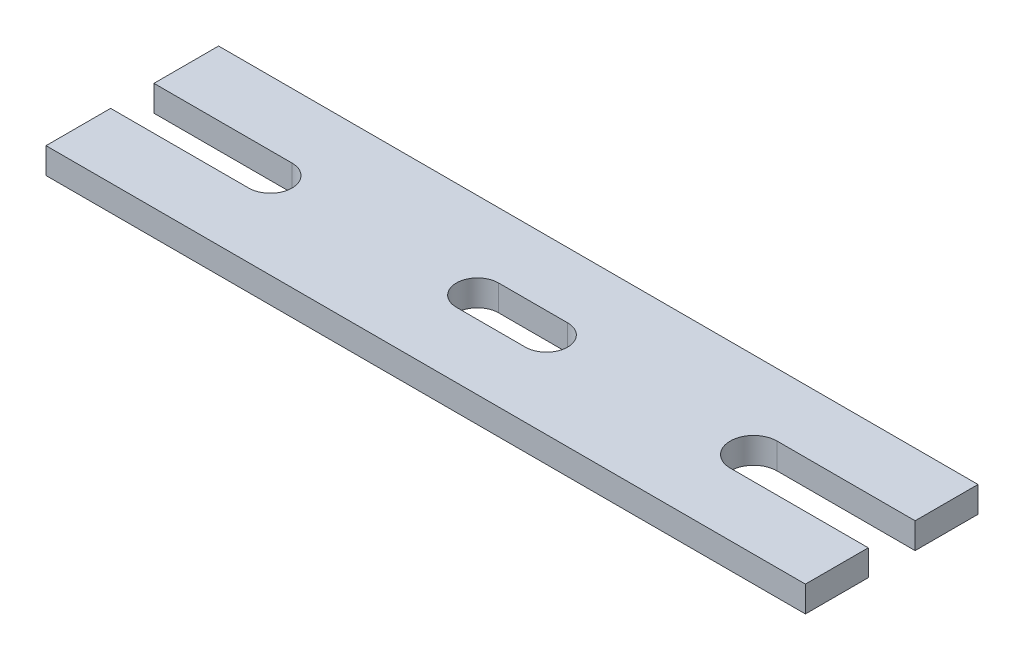
SolidWorks part; units mm, degrees
material "Plain Carbon Steel"
ref_plane "Front Plane" through (0, 0, 0) normal (0, 0, 1) x (1, 0, 0)
ref_plane "Top Plane" through (0, 0, 0) normal (0, 1, 0) x (1, 0, 0)
ref_plane "Right Plane" through (0, 0, 0) normal (1, 0, 0) x (0, 0, -1)
ref_plane "Plane12" through (88.9, 0, 0) normal (1, 0, 0) x (0, 0, -1)
ref_plane "Plane13" through (-88.9, 0, 0) normal (1, 0, 0) x (0, 0, -1)
sketch "Sketch1" plane through (0, 0, 0) normal (0, 1, 0) x (1, 0, 0)
  line L0 (-139.7, 0) -> (139.7, 0) construction
  line L1 (-139.7, 31.75) -> (139.7, 31.75)
  line L2 (-139.7, 31.75) -> (-139.7, -31.75)
  line L3 (-139.7, -31.75) -> (139.7, -31.75)
  line L4 (139.7, 31.75) -> (139.7, -31.75)
  line L5 (-139.7, 31.75) -> (139.7, -31.75) construction
  line L6 (-139.7, -31.75) -> (139.7, 31.75) construction
  point P0 (0, 0)
  dimension "D1" = 279.4
  dimension "D2" = 63.5
extrude "Boss-Extrude1" add sketch "Sketch1" along normal blind 9.525
sketch "Sketch9" plane through (0, 9.525, 0) normal (0, 1, 0) x (1, 0, 0)
  line L0 (-139.7, 31.75) -> (-139.7, -31.75) construction
  line L1 (-139.7, 7.97) -> (-88.9, 7.97)
  line L2 (-139.7, 7.97) -> (-139.7, -7.97)
  line L3 (-139.7, -7.97) -> (-88.9, -7.97)
  line L5 (-88.9, -5.2388) -> (-88.9, 5.2388) construction
  arc A0 (-88.9, 7.97) -> (-88.9, -7.97) centre (-88.9, 0) cw
  point P0 (-139.7, 0)
extrude "Cut-Extrude5" cut sketch "Sketch9" along direction (0, 1, 0) on the side against the normal through all
sketch "Sketch12" plane through (0, 9.525, 0) normal (0, 1, 0) x (1, 0, 0)
  line L0 (139.7, -31.75) -> (139.7, 31.75) construction
  line L1 (139.7, -8.6186) -> (88.9, -8.6186)
  line L2 (139.7, -8.6186) -> (139.7, 8.6186)
  line L3 (139.7, 8.6186) -> (88.9, 8.6186)
  line L5 (88.9, -5.2388) -> (88.9, 5.2388) construction
  arc A0 (88.9, -8.6186) -> (88.9, 8.6186) centre (88.9, 0) cw
  point P0 (139.7, 0)
extrude "Cut-Extrude7" cut sketch "Sketch12" against normal through all
sketch "Sketch13" plane through (0, 9.525, 0) normal (0, 1, 0) x (1, 0, 0)
  line L1 (-12.7, 7.7611) -> (12.7, 7.7611)
  line L3 (-12.7, -7.7611) -> (12.7, -7.7611)
  arc A0 (-12.7, 7.7611) -> (-12.7, -7.7611) centre (-12.7, 0) ccw
  arc A1 (12.7, -7.7611) -> (12.7, 7.7611) centre (12.7, 0) ccw
  point P0 (0, 0)
  dimension "D1" = 15.5222
extrude "Cut-Extrude8" cut sketch "Sketch13" against normal through all
